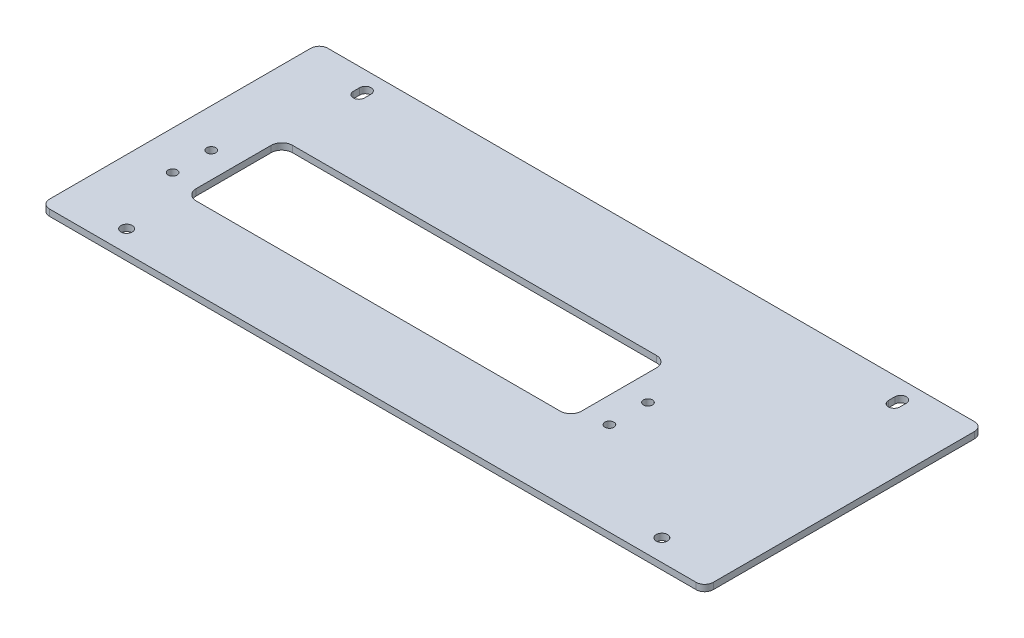
SolidWorks part; units mm, degrees
ref_plane "Front Plane" through (0, 0, 0) normal (0, 0, 1) x (1, 0, 0)
ref_plane "Top Plane" through (0, 0, 0) normal (0, 1, 0) x (1, 0, 0)
ref_plane "Right Plane" through (0, 0, 0) normal (1, 0, 0) x (0, 0, -1)
sketch "Sketch1" plane through (0, 0, 0) normal (0, 1, 0) x (1, 0, 0)
  line L1 (-155, -65) -> (155, -65)
  line L2 (-155, -65) -> (-155, 65)
  line L3 (-155, 65) -> (155, 65)
  line L4 (155, -65) -> (155, 65)
  line L5 (-155, -65) -> (155, 65) construction
  line L6 (-155, 65) -> (155, -65) construction
  point P0 (0, 0)
  dimension "D1" = 310
  dimension "D2" = 130
extrude "Boss-Extrude1" add sketch "Sketch1" along normal blind 3
fillet "Fillet1" radius 4 4 edges at (-155, 1.5, 65) (-155, 1.5, -65) (155, 1.5, -65) (155, 1.5, 65)
hole_wizard "Ø5.3 (5.3) Diameter Hole1" positions "Sketch4" profile "Sketch5" hole size "Ø5.3" standard "ANSI Metric" end condition through all
sketch "Sketch4" plane through (0, 3, 0) normal (0, 1, 0) x (1, 0, 0)
  line L1 (-125, -55) -> (125, -55)
  line L2 (-125, -55) -> (-125, 55)
  line L3 (-125, 55) -> (125, 55)
  line L4 (125, -55) -> (125, 55)
  line L5 (-125, -55) -> (125, 55) construction
  line L6 (-125, 55) -> (125, -55) construction
  line L7 (151, 65) -> (-151, 65) construction
  line L8 (155, -61) -> (155, 61) construction
  point P2 (125, 55)
  point P59 (-125, -55)
  point P60 (-125, 55)
  point P61 (125, -55)
  dimension "D1" = 10
  dimension "D2" = 30
sketch "Sketch5" plane through (125, 3, -55) normal (1, 0, 0) x (0, 0, 1)
  line L0 (0, 0) -> (0, 3)
  line L1 (0, 3) -> (2.65, 3)
  line L2 (2.65, 3) -> (2.65, 0)
  line L5 (2.65, 0) -> (0, 0)
  line L11 (0, -6.35) -> (0, 107.95) construction
  dimension "Thru Hole Dia." = 5.3
  dimension "Thru Hole Depth" = 3
sketch "Sketch6" plane through (0, 3, 0) normal (0, 1, 0) x (1, 0, 0)
  line L0 (0, 0) -> (-35, 0) construction
  line L1 (-125, -27.5) -> (55, -27.5)
  line L2 (-125, -27.5) -> (-125, 17.5)
  line L3 (-125, 17.5) -> (55, 17.5)
  line L4 (55, -27.5) -> (55, 17.5)
  line L5 (-125, -27.5) -> (55, 17.5) construction
  line L6 (-125, 17.5) -> (55, -27.5) construction
  line L7 (-35, -5) -> (-35, 0) construction
  point P0 (-35, -5)
  dimension "D1" = 45
  dimension "D2" = 180
  dimension "D3" = 5
  dimension "D4" = 35
extrude "Cut-Extrude1" cut sketch "Sketch6" against normal through all
fillet "Fillet2" radius 5 4 edges at (55, 1.5, 27.5) (-125, 1.5, 27.5) (55, 1.5, -17.5) (-125, 1.5, -17.5)
hole_wizard "M5x0.8 Tapped Hole1" positions "Sketch7" profile "Sketch8" tap size "M5x0.8" standard "ANSI Metric" end condition through all
sketch "Sketch7" plane through (0, 3, 0) normal (0, 1, 0) x (1, 0, 0)
  line L1 (-137, -21.5) -> (67, -21.5) construction
  line L2 (-137, -21.5) -> (-137, -3.5) construction
  line L3 (-137, -3.5) -> (67, -3.5) construction
  line L4 (67, -21.5) -> (67, -3.5) construction
  line L5 (-137, -21.5) -> (67, -3.5) construction
  line L6 (-137, -3.5) -> (67, -21.5) construction
  line L8 (-151, -65) -> (151, -65) construction
  line L9 (-35, 65) -> (-35, -65) construction
  line L10 (151, 65) -> (-151, 65) construction
  line L11 (-35, -3.5) -> (-35, -21.5) construction
  point P2 (67, -3.5)
  point P137 (-137, -21.5)
  point P138 (-137, -3.5)
  point P139 (67, -21.5)
  dimension "D4" = 35
  dimension "D1" = 18
  dimension "D2" = 204
  dimension "D3" = 43.5
sketch "Sketch8" plane through (67, 3, 3.5) normal (1, 0, 0) x (0, 0, 1)
  line L0 (0, 0) -> (0, 3)
  line L1 (0, 3) -> (2.1, 3)
  line L2 (2.1, 3) -> (2.1, 0)
  line L5 (2.1, 0) -> (0, 0)
  line L11 (0, -6.35) -> (0, 107.95) construction
  dimension "Thru Tap Drill Dia." = 4.2
  dimension "Thru Tap Drill Depth" = 3
cosmetic thread "Hole Thread2" parameters "D2"=5
cosmetic thread "Hole Thread3" parameters "D2"=5
cosmetic thread "Hole Thread4" parameters "D2"=5
cosmetic thread "Hole Thread5" parameters "D2"=5
sketch "Sketch9" plane through (0, 3, 0) normal (0, 1, 0) x (1, 0, 0)
  line L0 (-125, 53.5) -> (-125, 56.5) construction
  line L1 (-127.65, 53.5) -> (-127.65, 56.5)
  line L2 (-122.35, 53.5) -> (-122.35, 56.5)
  line L3 (125, 53.5) -> (125, 56.5) construction
  line L4 (122.35, 53.5) -> (122.35, 56.5)
  line L5 (127.65, 53.5) -> (127.65, 56.5)
  arc A0 (-127.65, 53.5) -> (-122.35, 53.5) centre (-125, 53.5) ccw
  arc A1 (-122.35, 56.5) -> (-127.65, 56.5) centre (-125, 56.5) ccw
  arc A2 (122.35, 53.5) -> (127.65, 53.5) centre (125, 53.5) ccw
  arc A3 (127.65, 56.5) -> (122.35, 56.5) centre (125, 56.5) ccw
  circle A4 centre (-125, 55) radius 2.65 construction
  point P2 (-125, 55)
  point P9 (125, 55)
  dimension "D1" = 3
extrude "Cut-Extrude2" cut sketch "Sketch9" against normal through all
equation "\"Shift\"= 35"
equation "\"D4@Sketch6\"=\"Shift\""
equation "\"D4@Sketch7\"=\"Shift\""
